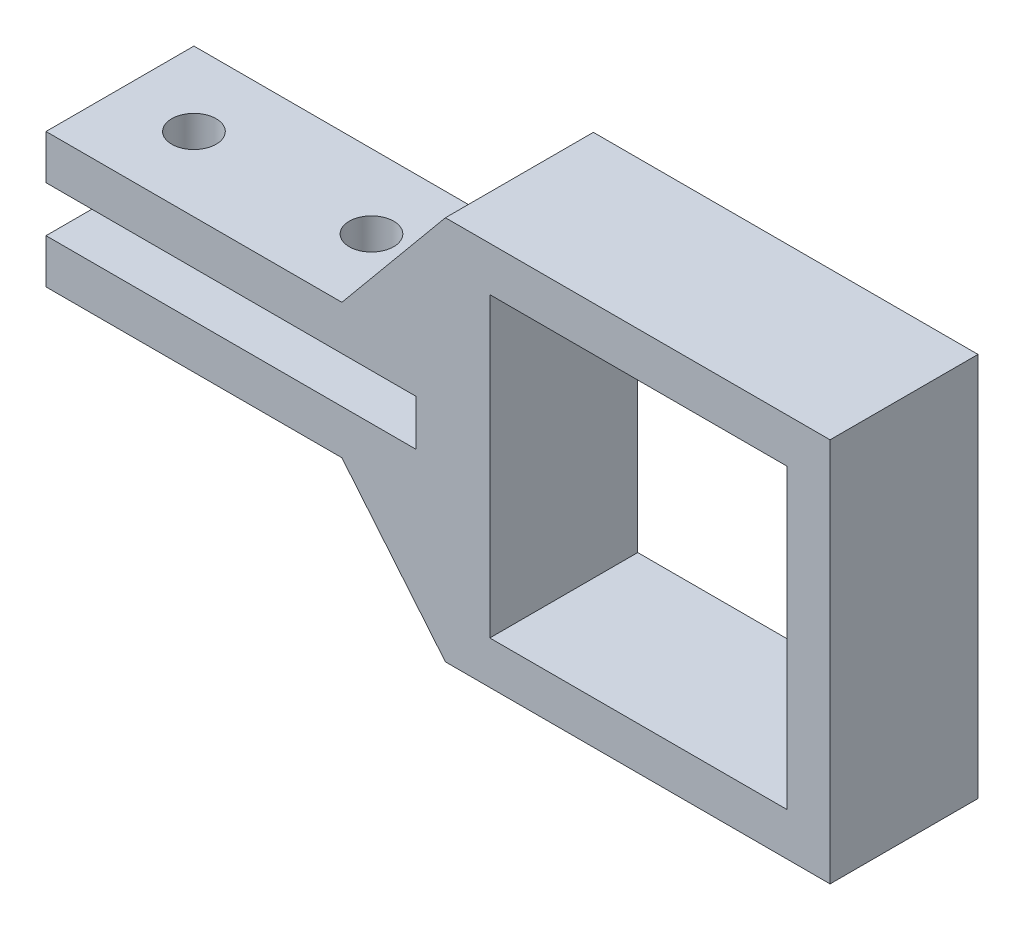
SolidWorks part; units mm, degrees
ref_plane "前视基准面" through (0, 0, 0) normal (0, 0, 1) x (1, 0, 0)
ref_plane "上视基准面" through (0, 0, 0) normal (0, 1, 0) x (1, 0, 0)
ref_plane "右视基准面" through (0, 0, 0) normal (1, 0, 0) x (0, 0, -1)
sketch "草图1" plane through (0, 0, 0) normal (0, 0, 1) x (1, 0, 0)
  line L68 (-21.1315, 0) -> (10.2214, 0) construction
  line L78 (-27, 4.55) -> (-27, 1.55)
  line L79 (-27, 4.55) -> (-7, 4.55)
  line L82 (-27, 1.55) -> (-2, 1.55)
  line L83 (0, 4.55) -> (0, 13) construction
  line L84 (0, 13) -> (26, 13)
  line L85 (0, -13) -> (26, -13)
  line L86 (0, -4.55) -> (0, -13) construction
  line L87 (-27, -1.55) -> (-2, -1.55)
  line L90 (-27, -4.55) -> (-7, -4.55)
  line L91 (-27, -4.55) -> (-27, -1.55)
  line L92 (-2, 1.55) -> (-2, -1.55)
  line L93 (26, 13) -> (26, -13)
  line L94 (0, 1.55) -> (0, 4.55) construction
  line L95 (0, -1.55) -> (0, -4.55) construction
  line L96 (0, -13) -> (-7, -4.55)
  line L97 (0, 13) -> (-7, 4.55)
  line L98 (-7, 4.55) -> (0, 4.55) construction
  line L99 (-7, -4.55) -> (0, -4.55) construction
  dimension "D1" = 27
  dimension "D2" = 26
  dimension "D3" = 3.1
  dimension "D4" = 25
  dimension "D5" = 7
  dimension "D6" = 7
  dimension "D8" = 26
  dimension "5" = 3
extrude "凸台-拉伸1" add sketch "草图1" along normal blind 10 contours L85 L93 L84 L97 L79 L78 L82 L92 L87 L91 L90 L96
sketch "草图5" plane through (0, 0, 10) normal (0, 0, 1) x (1, 0, 0)
  line L0 (3, 10) -> (3, -10.1)
  line L1 (3, -10.1) -> (23.1, -10.1)
  line L3 (23.1, 10) -> (3, 10)
  line L17 (23.1, 10) -> (23.1, -10.1)
  dimension "D1" = 20.1
  dimension "D2" = 20.1
extrude "切除-拉伸1" cut sketch "草图5" against normal blind 30
sketch "草图7" plane through (0, 4.55, 0) normal (0, 1, 0) x (1, 0, 0)
  line L0 (-22, -5) -> (-27, -5) construction
  line L2 (-27, -10) -> (-27, 0) construction
  line L3 (-22, -5) -> (-22, 0) construction
  line L4 (-27, 0) -> (-7, 0) construction
  circle A0 centre (-22, -5) radius 1.5
  circle A1 centre (-10, -5) radius 1.5
  dimension "D1" = 3
  dimension "D2" = 5
  dimension "D3" = 5
  dimension "D5" = 12
  dimension "D4" = 2
extrude "切除-拉伸5" cut sketch "草图7" against normal up to surface (9.1 mm away) up to face at (-17, -4.55, 5)
